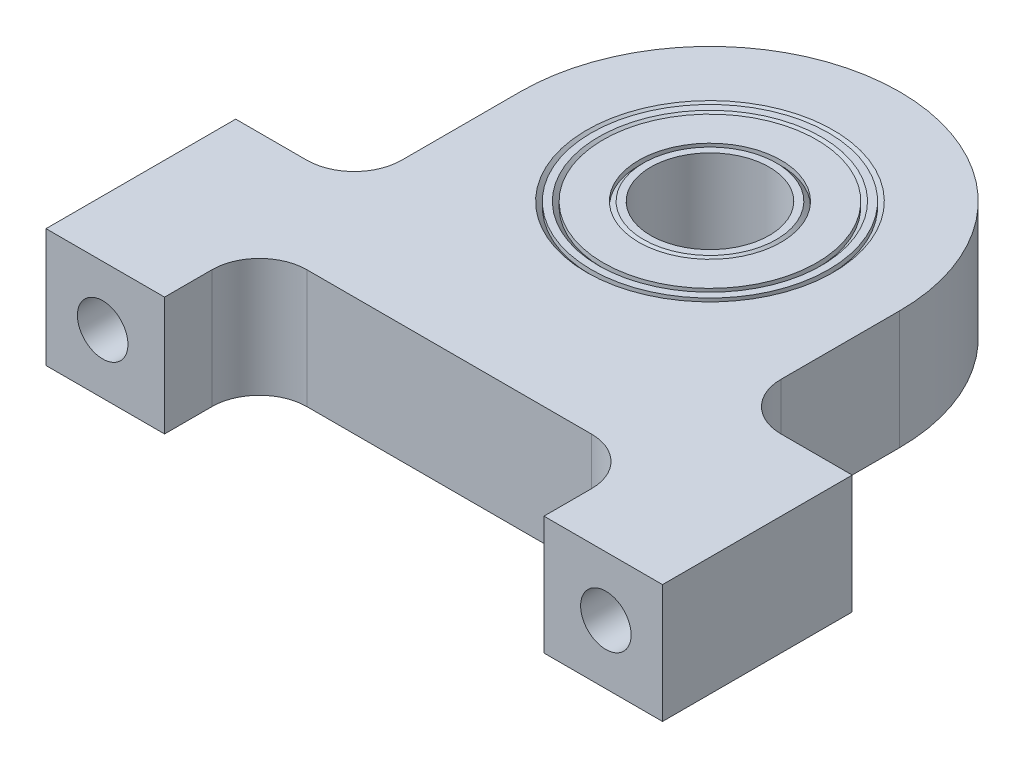
SolidWorks part; units mm, degrees
material "6061 Alloy"
ref_plane "Front Plane" through (0, 0, 0) normal (0, 0, 1) x (1, 0, 0)
ref_plane "Top Plane" through (0, 0, 0) normal (0, 1, 0) x (1, 0, 0)
ref_plane "Right Plane" through (0, 0, 0) normal (1, 0, 0) x (0, 0, -1)
sketch "Sketch1" plane through (0, 0, 0) normal (0, 1, 0) x (1, 0, 0)
  line L0 (-10.16, 0) -> (-10.16, -6.35)
  line L1 (-16.51, -19.05) -> (-10.16, -19.05)
  line L2 (-16.51, -19.05) -> (-16.51, -8.89)
  line L3 (-16.51, -8.89) -> (-12.7, -8.89)
  line L4 (16.51, -19.05) -> (16.51, -8.89)
  line L5 (10.16, 0) -> (10.16, -6.35)
  line L6 (12.7, -8.89) -> (16.51, -8.89)
  line L7 (-10.16, -19.05) -> (-10.16, -16.51)
  line L8 (-7.62, -13.97) -> (7.62, -13.97)
  line L9 (10.16, -16.51) -> (10.16, -19.05)
  line L10 (10.16, -19.05) -> (16.51, -19.05)
  circle A0 centre (0, 0) radius 3.175 construction
  arc A1 (10.16, 0) -> (-10.16, 0) centre (0, 0) ccw
  arc A2 (10.16, -6.35) -> (12.7, -8.89) centre (12.7, -6.35) ccw
  arc A3 (-10.16, -6.35) -> (-12.7, -8.89) centre (-12.7, -6.35) cw
  arc A4 (7.62, -13.97) -> (10.16, -16.51) centre (7.62, -16.51) cw
  arc A5 (-10.16, -16.51) -> (-7.62, -13.97) centre (-7.62, -16.51) cw
  point P13 (10.16, -8.89)
  point P24 (-10.16, -13.97)
  dimension "D1" = 33.02
  dimension "D5" = 6.35
  dimension "D6" = 20.32
  dimension "D7" = 2.54
  dimension "D8" = 5.08
  dimension "D9" = 2.54
  dimension "D2" = 16.51
  dimension "D3" = 19.05
  dimension "D4" = 10.16
extrude "Boss-Extrude1" add sketch "Sketch1" along normal blind 6.35
sketch "Sketch2" plane through (0, 6.35, 0) normal (0, 1, 0) x (1, 0, 0)
  circle A0 centre (0, 0) radius 6.35
  dimension "D1" = 12.7
extrude "Cut-Extrude1" cut sketch "Sketch2" against normal blind 4.7625
sketch "Sketch3" plane through (0, 1.5875, 0) normal (0, 1, 0) x (1, 0, 0)
  circle A0 centre (0, 0) radius 5.08
extrude "Cut-Extrude2" cut sketch "Sketch3" against normal up to next
chamfer "Chamfer1" distance 0.254 angle 45 1 edges at (0, 6.35, 6.35)
ref_plane "Plane1" through (0, 1.5875, 0) normal (0, 1, 0) x (-1, 0, 0)
sketch "Sketch4" plane through (0, 1.5875, 0) normal (0, 1, 0) x (1, 0, 0)
  circle A0 centre (0, 0) radius 6.35
  circle A1 centre (0, 0) radius 5.715
  dimension "D1" = 0.635
extrude "Boss-Extrude2" add sketch "Sketch4" along normal blind 4.7625
chamfer "Chamfer2" distance 0.254 angle 45 2 edges at (0, 6.35, 5.715) (0, 1.5875, 5.715)
sketch "Sketch5" plane through (0, 1.5875, 0) normal (0, 1, 0) x (-1, 0, 0)
  circle A0 centre (0, 0) radius 3.175
  circle A1 centre (0, 0) radius 3.81
  dimension "D1" = 0.635
extrude "Boss-Extrude3" add sketch "Sketch5" along normal blind 4.7625 separate body
chamfer "Chamfer3" distance 0.254 angle 45 2 edges at (0, 1.5875, 3.81) (0, 6.35, 3.81)
ref_plane "Plane2" through (0, 6.35, 0) normal (0, 1, 0) x (-1, 0, 0)
sketch "Sketch7" plane through (0, 6.35, 0) normal (0, 1, 0) x (-1, 0, 0)
  circle A0 centre (0, 0) radius 3.81
  circle A1 centre (0, 0) radius 5.715
extrude "Boss-Extrude4" add sketch "Sketch7" against normal blind 4.2545
hole_wizard "#6-32 Tapped Hole1" positions "Sketch9" profile "Sketch8" tap size "#6-32" standard "Ansi Inch"
sketch "Sketch9" plane through (0, 0, 19.05) normal (0, 0, 1) x (1, 0, 0)
  line L0 (-16.51, 0) -> (-10.16, 0) construction
  line L1 (10.16, 0) -> (16.51, 0) construction
  point P0 (-13.4747, 3.175)
  point P1 (13.4747, 3.175)
  dimension "D1" = 3.175
  dimension "D2" = 3.175
  dimension "D3" = 26.9494
  dimension "D4" = 13.4747
sketch "Sketch8" plane through (-13.4747, 3.175, 19.05) normal (1, 0, 0) x (0, -1, 0)
  line L0 (0, 0) -> (0, 8.4327)
  line L1 (0, 8.4327) -> (1.3525, 7.62)
  line L2 (1.3525, 7.62) -> (1.3525, 0)
  line L5 (1.3525, 0) -> (0, 0)
  line L10 (0, 8.4327) -> (-1.3526, 7.62) construction
  line L11 (0, -6.35) -> (0, 107.95) construction
  dimension "Tap Drill Dia." = 2.7051
  dimension "Tap Drill Depth" = 7.62
  dimension "Drill Angle" = 118
cosmetic thread "Hole Thread1" parameters "D1"=7.0104, "D2"=3.5052
cosmetic thread "Hole Thread2" parameters "D1"=7.0104, "D2"=3.5052
